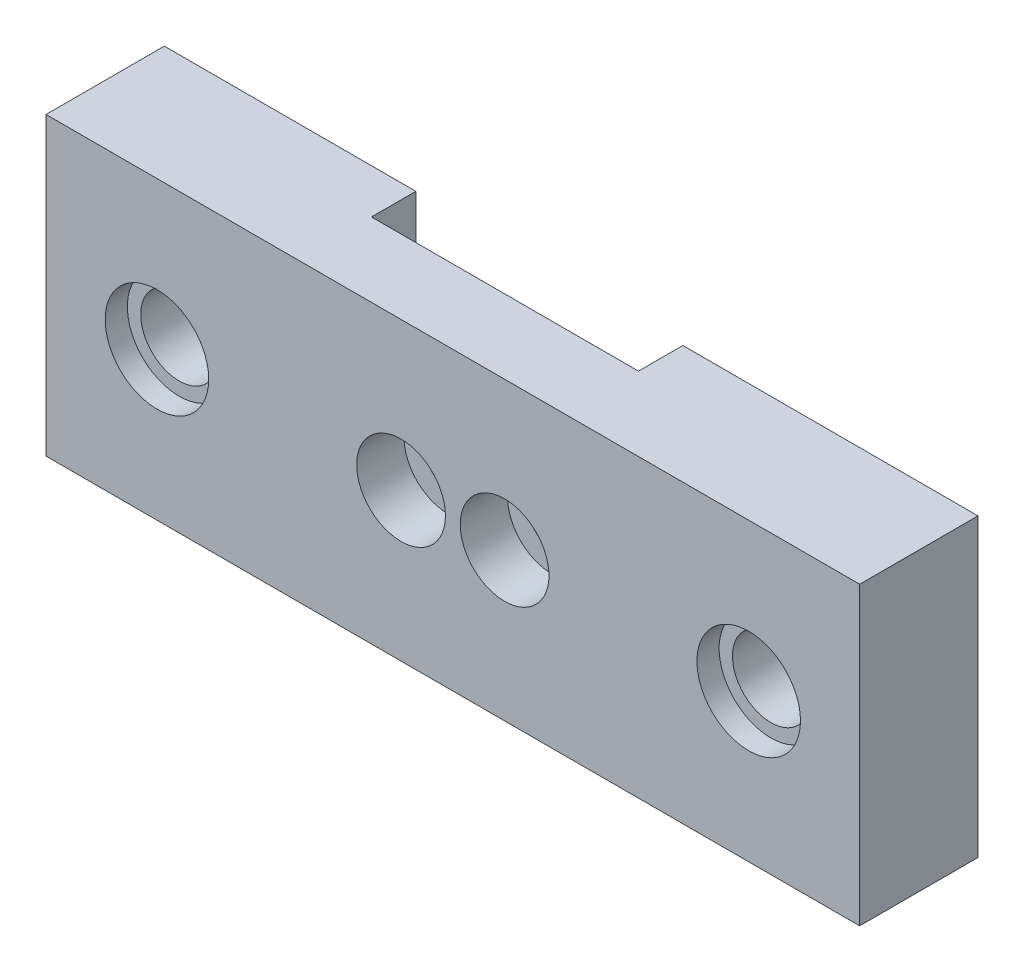
SolidWorks part; units mm, degrees
ref_plane "Plan de face" through (0, 0, 0) normal (0, 0, 1) x (1, 0, 0)
ref_plane "Plan de dessus" through (0, 0, 0) normal (0, 1, 0) x (1, 0, 0)
ref_plane "Plan de droite" through (0, 0, 0) normal (1, 0, 0) x (0, 0, -1)
sketch "Esquisse1" plane through (0, 0, 0) normal (0, 0, 1) x (1, 0, 0)
  line L0 (0, 10) -> (0, 0) construction
  line L1 (-27.5, 10) -> (27.5, 10)
  line L2 (-27.5, 10) -> (-27.5, -10)
  line L3 (-27.5, -10) -> (27.5, -10)
  line L4 (27.5, 10) -> (27.5, -10)
  line L5 (0, 0) -> (-27.5, 0) construction
  line L6 (0, 0) -> (20, 0) construction
  circle A0 centre (-20, 0) radius 2.6
  circle A1 centre (20, 0) radius 2.6
  circle A2 centre (-3.5, 0) radius 1.55
  circle A3 centre (3.5, 0) radius 1.55
  dimension "D3" = 5.2
  dimension "D4" = 40
  dimension "D6" = 3.1
  dimension "D7" = 7
  dimension "D8" = 3.5
  dimension "D1" = 55
  dimension "D2" = 20
  dimension "D5" = 20
extrude "Extrusion1" add sketch "Esquisse1" along normal blind 8
sketch "Esquisse2" plane through (0, 0, 8) normal (0, 0, 1) x (1, 0, 0)
  circle A0 centre (-20, 0) radius 3.5
  circle A1 centre (20, 0) radius 3.5
  dimension "D1" = 7
extrude "Enlèv. mat.-Extru.1" cut sketch "Esquisse2" against normal blind 1.5
sketch "Esquisse3" plane through (0, 0, 8) normal (0, 0, 1) x (1, 0, 0)
  circle A0 centre (-3.5, 0) radius 3
  circle A1 centre (3.5, 0) radius 3
  dimension "D1" = 6
extrude "Enlèv. mat.-Extru.2" cut sketch "Esquisse3" against normal blind 3.2
sketch "Esquisse4" plane through (0, 0, 0) normal (0, 0, -1) x (-1, 0, 0)
  line L0 (-7.55, -10) -> (-7.55, 10)
  line L1 (27.5, -10) -> (-27.5, -10) construction
  line L2 (-27.5, 10) -> (27.5, 10) construction
  line L3 (7.55, -10) -> (7.55, 3.0004)
  line L4 (10.5, 6) -> (10.5, 10)
  arc A0 (7.55, 3.0004) -> (10.5, 6) centre (7.5, 6) ccw
  circle M1 centre (3.5, 0) radius 1.55
  line M4 (27.5, 10) -> (-27.5, 10)
  line M6 (-27.5, -10) -> (27.5, -10)
  circle M8 centre (-3.5, 0) radius 1.55
  dimension "D4" = 3
  dimension "D1" = 7.55
  dimension "D2" = 7.55
  dimension "D3" = 7.5
  dimension "D5" = 4
extrude "Enlèv. mat.-Extru.3" cut sketch "Esquisse4" against normal blind 3 contours L3 A0 L4 L0 M4 M6 M1 M8
